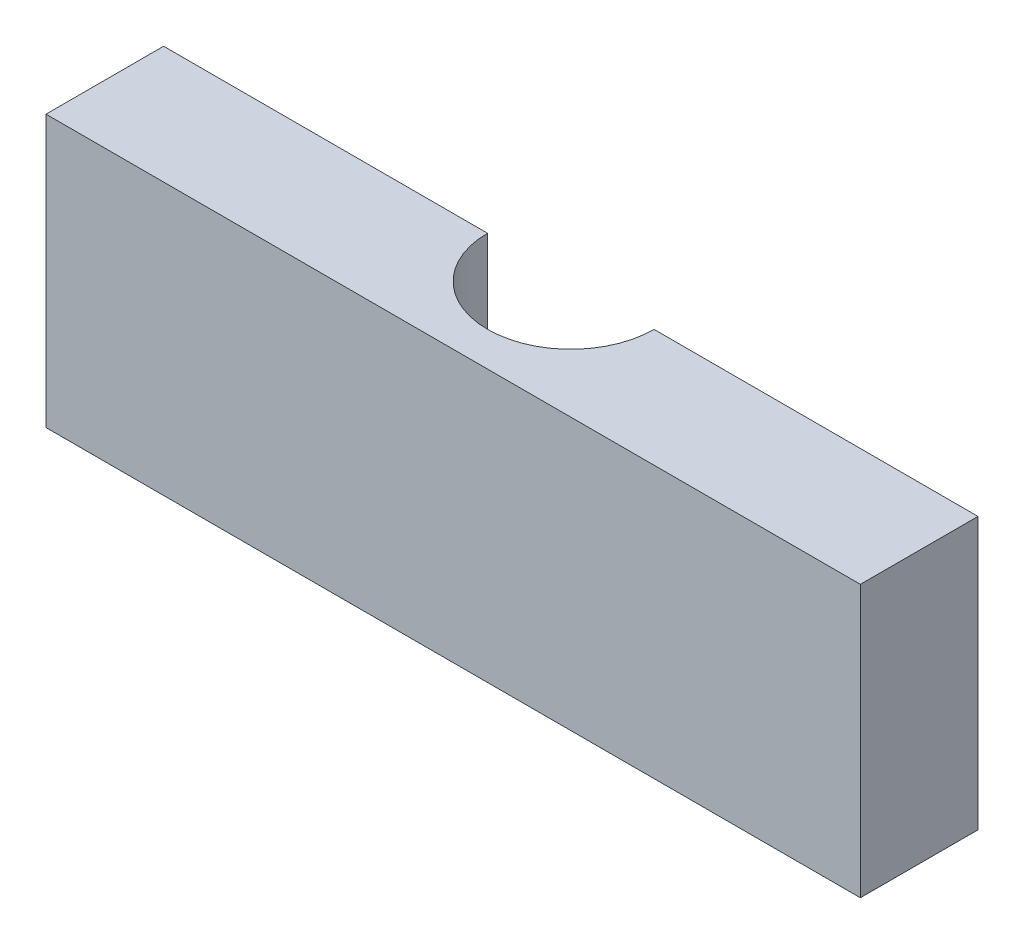
SolidWorks part; units mm, degrees
ref_plane "前视基准面" through (0, 0, 0) normal (0, 0, 1) x (1, 0, 0)
ref_plane "上视基准面" through (0, 0, 0) normal (0, 1, 0) x (1, 0, 0)
ref_plane "右视基准面" through (0, 0, 0) normal (1, 0, 0) x (0, 0, -1)
sketch "草图1" plane through (0, 0, 0) normal (0, 0, 1) x (1, 0, 0)
  line L1 (-13.9979, 2.2077) -> (31.0021, 2.2077)
  line L2 (-13.9979, 2.2077) -> (-13.9979, -12.7923)
  line L3 (-13.9979, -12.7923) -> (31.0021, -12.7923)
  line L4 (31.0021, 2.2077) -> (31.0021, -12.7923)
  dimension "D1" = 45
  dimension "D2" = 15
extrude "凸台-拉伸1" add sketch "草图1" along normal blind 6.5
sketch "草图3" plane through (0, 2.2077, 0) normal (0, 1, 0) x (1, 0, 0)
  line L0 (31.0021, 0) -> (-13.9979, 0) construction
  circle A0 centre (8.5021, 0) radius 4.6
  dimension "D1" = 9.2
extrude "切除-拉伸1" cut sketch "草图3" against normal through all
